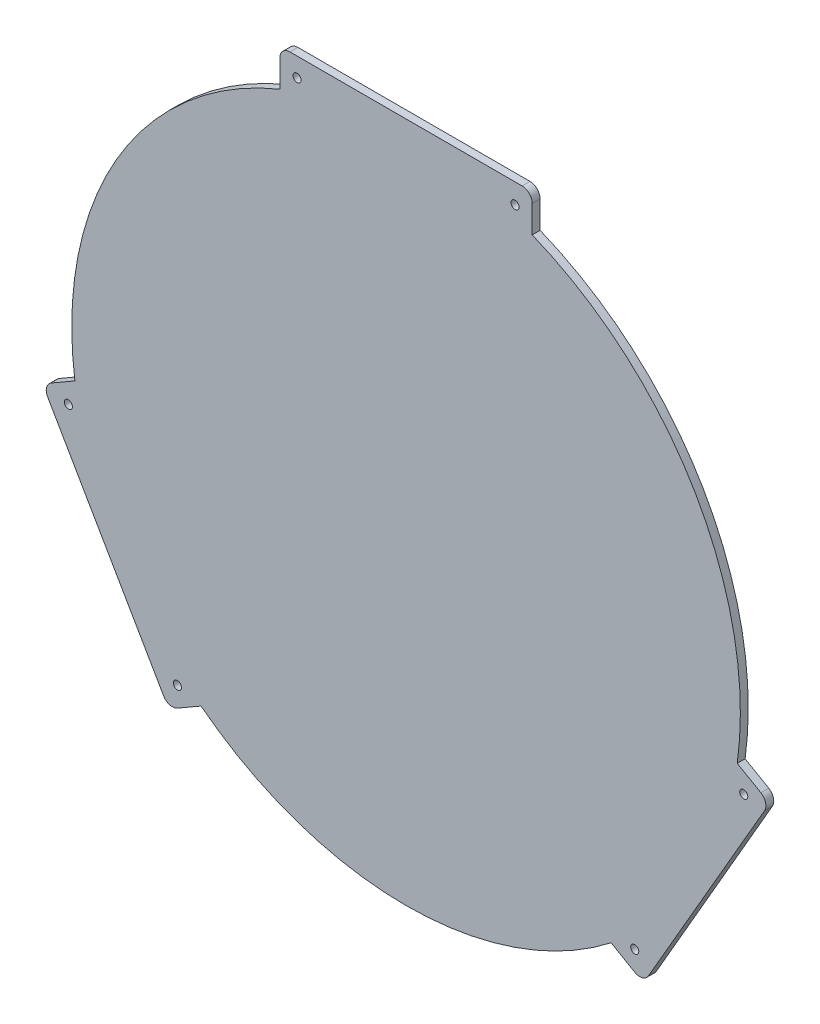
SolidWorks part; units mm, degrees
ref_plane "Front Plane" through (0, 0, 0) normal (0, 0, 1) x (1, 0, 0)
ref_plane "Top Plane" through (0, 0, 0) normal (0, 1, 0) x (1, 0, 0)
ref_plane "Right Plane" through (0, 0, 0) normal (1, 0, 0) x (0, 0, -1)
sketch "Model" plane through (0, 0, 0) normal (0, 0, 1) x (1, 0, 0)
  line L0 (105.3, 249.9134) -> (191.7, 249.5134) construction
  line L1 (194.5, 257.4134) -> (102.5, 257.4134)
  line L2 (98.5, 253.4134) -> (98.5, 242.6173)
  line L3 (198.5, 253.4134) -> (198.5, 242.6173)
  line L4 (52.4215, 11.3263) -> (6.4215, 91.0006)
  line L6 (7.8856, 96.4647) -> (17.2353, 101.8627)
  line L7 (57.8856, 9.8622) -> (67.2353, 15.2602)
  line L9 (244.5785, 11.3263) -> (290.5785, 91.0006)
  line L10 (289.1144, 96.4647) -> (279.7647, 101.8627)
  line L11 (239.1144, 9.8622) -> (229.7647, 15.2602)
  arc A0 (102.5, 257.4134) -> (98.5, 253.4134) centre (102.5, 253.4134) ccw
  arc A1 (198.5, 253.4134) -> (194.5, 257.4134) centre (194.5, 253.4134) ccw
  circle A2 centre (105.3, 249.9134) radius 1.6
  circle A3 centre (191.7, 249.5134) radius 1.6
  arc A4 (7.8856, 96.4647) -> (6.4215, 91.0006) centre (9.8856, 93.0006) ccw
  arc A5 (52.4215, 11.3263) -> (57.8856, 9.8622) centre (55.8856, 13.3263) ccw
  arc A6 (290.5785, 91.0006) -> (289.1144, 96.4647) centre (287.1144, 93.0006) ccw
  arc A7 (239.1144, 9.8622) -> (244.5785, 11.3263) centre (241.1144, 13.3263) ccw
  circle A8 centre (282.3369, 92.5257) radius 1.6
  circle A9 centre (239.1369, 17.7011) radius 1.6
  arc A10 (279.7647, 101.8627) -> (198.5, 242.6173) centre (148.5, 119.9134) ccw
  arc A11 (98.5, 242.6173) -> (17.2353, 101.8627) centre (148.5, 119.9134) ccw
  arc A12 (67.2353, 15.2602) -> (229.7647, 15.2602) centre (148.5, 119.9134) ccw
  circle A13 centre (14.6631, 92.5257) radius 1.6
  circle A14 centre (57.8631, 17.7011) radius 1.6
  circle A15 centre (148.5, 119.9134) radius 137.5 construction
  circle A16 centre (148.5, 119.9134) radius 145.2029 construction
  dimension "D1" = 100
  dimension "D3" = 3.2
  dimension "D4" = 4
  dimension "D6" = 6.8
  dimension "D7" = 7.9
  dimension "D8" = 275
  dimension "D9" = 5
  dimension "D10" = 74.8246
  dimension "D2" = 92
  dimension "D5" = 10.7961
extrude "Boss-Extrude1" add sketch "Model" along normal blind 3.125
